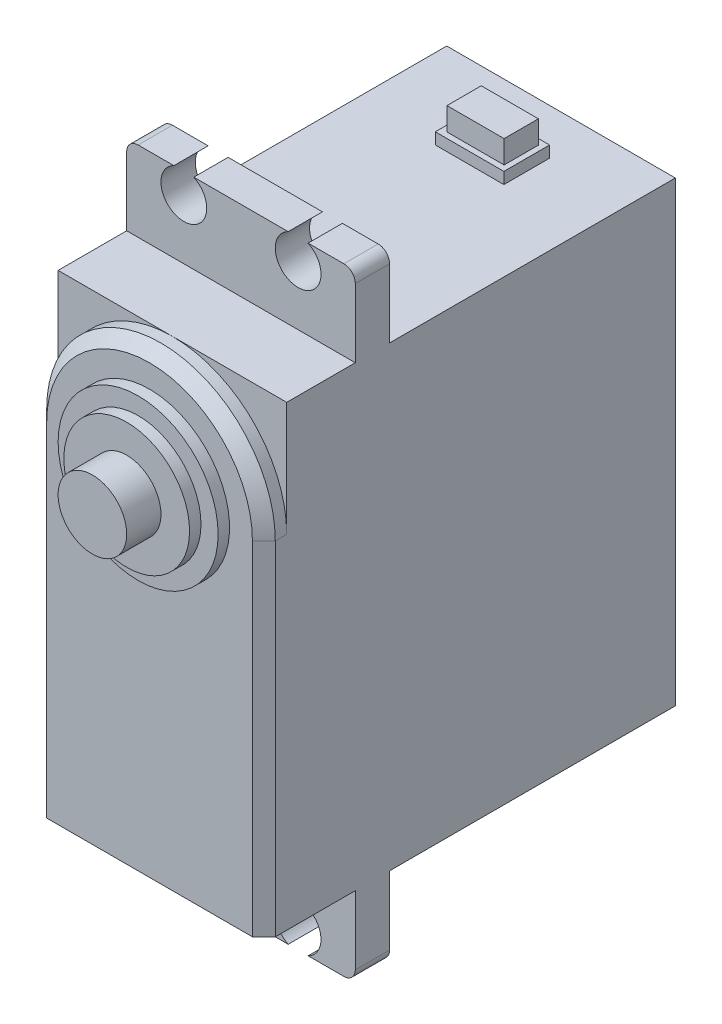
SolidWorks part; units mm, degrees
ref_plane "Front Plane" through (0, 0, 0) normal (0, 0, 1) x (1, 0, 0)
ref_plane "Top Plane" through (0, 0, 0) normal (0, 1, 0) x (1, 0, 0)
ref_plane "Right Plane" through (0, 0, 0) normal (1, 0, 0) x (0, 0, -1)
sketch "Sketch1" plane through (0, 0, 0) normal (0, 0, 1) x (1, 0, 0)
  line L1 (-10, -20) -> (10, -20)
  line L2 (-10, -20) -> (-10, 20)
  line L3 (-10, 20) -> (10, 20)
  line L4 (10, -20) -> (10, 20)
  line L5 (-10, -20) -> (10, 20) construction
  line L6 (-10, 20) -> (10, -20) construction
  point P0 (0, 0)
  dimension "D1" = 20
  dimension "D2" = 40
extrude "Boss-Extrude1" add sketch "Sketch1" along normal blind 36
chamfer "Chamfer1" distance 2 angle 45 4 edges at (0, 20, 0) (-10, 0, 0) (0, -20, 0) (10, 0, 0)
ref_plane "Plane1" through (0, 0, 27) normal (0, 0, 1) x (1, 0, 0)
sketch "Sketch2" plane through (0, 0, 27) normal (0, 0, 1) x (1, 0, 0)
  line L0 (-10, 25.2) -> (10, 25.2) construction
  line L1 (-10, 20) -> (10, 20)
  line L2 (-10, 20) -> (-10, 27)
  line L3 (-10, 27) -> (-5.8718, 27)
  line L4 (10, 20) -> (10, 27)
  line L5 (-4.1282, 27) -> (4.1282, 27)
  line L6 (5.8718, 27) -> (10, 27)
  line L9 (0, 34) -> (0, 20) construction
  arc A0 (4.1282, 27) -> (5.8718, 27) centre (5, 25.2) ccw
  arc A1 (-5.8718, 27) -> (-4.1282, 27) centre (-5, 25.2) ccw
  dimension "D4" = 4
  dimension "D5" = 4
  dimension "D1" = 7
  dimension "D3" = 1.8
  dimension "D11" = 5
  dimension "D12" = 5
extrude "Boss-Extrude7" add sketch "Sketch2" along normal blind 3
fillet "Fillet1" radius 1 2 edges at (10, 27, 28.5) (-10, 27, 28.5)
mirror "Mirror1" about plane through (0, 0, 0) normal (0, 1, 0) of "Boss-Extrude7"
fillet "Fillet2" radius 1 2 edges at (-10, -27, 28.5) (10, -27, 28.5)
sketch "Sketch3" plane through (0, 20, 0) normal (0, 1, 0) x (1, 0, 0)
  line L0 (0, 0) -> (0, -27) construction
  line L1 (-11, -27) -> (11, -27) construction
  line L2 (-8, 0) -> (8, 0) construction
  line L3 (-3, -6) -> (3, -6)
  line L4 (-3, -6) -> (-3, -10)
  line L5 (-3, -10) -> (3, -10)
  line L6 (3, -6) -> (3, -10)
  line L7 (-3, -6) -> (3, -10) construction
  line L8 (-3, -10) -> (3, -6) construction
  point P5 (0, -8)
  dimension "D1" = 4
  dimension "D2" = 8
  dimension "D3" = 6
extrude "Boss-Extrude8" add sketch "Sketch3" along normal blind 1
sketch "Sketch4" plane through (0, 21, 0) normal (0, 1, 0) x (1, 0, 0)
  line L1 (-2.4752, -6.5043) -> (2.5248, -6.5043)
  line L2 (-2.4752, -6.5043) -> (-2.4752, -9.5043)
  line L3 (-2.4752, -9.5043) -> (2.5248, -9.5043)
  line L4 (2.5248, -6.5043) -> (2.5248, -9.5043)
  line L5 (-2.4752, -6.5043) -> (2.5248, -9.5043) construction
  line L6 (-2.4752, -9.5043) -> (2.5248, -6.5043) construction
  point P0 (0.0248, -8.0043)
  dimension "D1" = 5
  dimension "D2" = 3
extrude "Boss-Extrude9" add sketch "Sketch4" along normal blind 2
sketch "Sketch5" plane through (0, 0, 36) normal (0, 0, 1) x (1, 0, 0)
  line L0 (0, 20) -> (0, -20) construction
  line L1 (-10, 20) -> (10, 20) construction
  line L2 (-10, -20) -> (10, -20) construction
  line L3 (-10, 20) -> (-10, -20) construction
  line L4 (10, -20) -> (10, 20) construction
  line L5 (-10, 10) -> (-10, -20)
  line L6 (-10, -20) -> (10, -20)
  line L7 (10, -20) -> (10, 10)
  line L8 (10, 20) -> (-10, 20) construction
  arc A0 (-10, 10) -> (10, 10) centre (0, 10) cw
  dimension "D1" = 10
extrude "Boss-Extrude10" add sketch "Sketch5" along normal blind 2
chamfer "Chamfer2" distance 1 angle 45 3 edges at (10, -5, 38) (0, 20, 38) (-10, -5, 38)
sketch "Sketch6" plane through (0, 0, 38) normal (0, 0, 1) x (1, 0, 0)
  line L0 (-9, -20) -> (9, -20) construction
  circle A0 centre (0, 10) radius 7
  dimension "D1" = 14
  dimension "D2" = 30
extrude "Boss-Extrude11" add sketch "Sketch6" along normal blind 1
sketch "Sketch7" plane through (0, 0, 39) normal (0, 0, 1) x (1, 0, 0)
  circle A0 centre (0, 10) radius 5.5
  dimension "D1" = 11
extrude "Boss-Extrude12" add sketch "Sketch7" along normal blind 1
sketch "Sketch8" plane through (0, 0, 40) normal (0, 0, 1) x (1, 0, 0)
  circle A0 centre (0, 10) radius 3
  dimension "D1" = 6
extrude "Boss-Extrude13" add sketch "Sketch8" along normal blind 3
